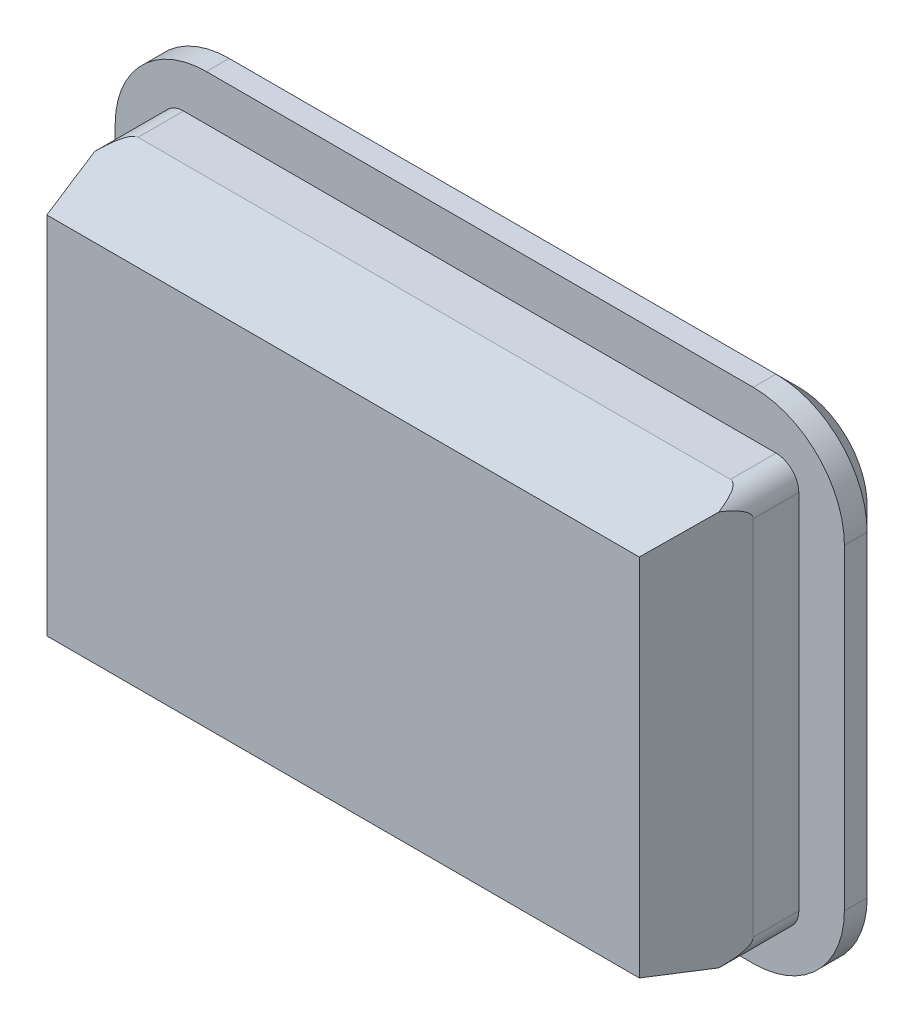
SolidWorks part; units mm, degrees
ref_plane "Front Plane" through (0, 0, 0) normal (0, 0, 1) x (1, 0, 0)
ref_plane "Top Plane" through (0, 0, 0) normal (0, 1, 0) x (1, 0, 0)
ref_plane "Right Plane" through (0, 0, 0) normal (1, 0, 0) x (0, 0, -1)
sketch "Sketch1" plane through (0, 0, 0) normal (0, 0, 1) x (1, 0, 0)
  line L1 (-7, -4.475) -> (7, -4.475)
  line L2 (-7, -4.475) -> (-7, 4.475)
  line L3 (-7, 4.475) -> (7, 4.475)
  line L4 (7, -4.475) -> (7, 4.475)
  line L5 (-7, -4.475) -> (7, 4.475) construction
  line L6 (-7, 4.475) -> (7, -4.475) construction
  point P0 (0, 0)
  dimension "D1" = 14
  dimension "D2" = 8.95
ref_plane "Plane1" through (0, 0, 2) normal (0, 0, 1) x (1, 0, 0)
sketch "Sketch2" plane through (0, 0, 2) normal (0, 0, 1) x (1, 0, 0)
  line L1 (-6.5, -4) -> (6.5, -4)
  line L2 (-6.5, -4) -> (-6.5, 4)
  line L3 (-6.5, 4) -> (6.5, 4)
  line L4 (6.5, -4) -> (6.5, 4)
  line L5 (-6.5, -4) -> (6.5, 4) construction
  line L6 (-6.5, 4) -> (6.5, -4) construction
  point P0 (0, 0)
  dimension "D1" = 13
  dimension "D2" = 8
loft "Loft1" add profiles "Sketch2", "Sketch1"
sketch "Sketch3" plane through (0, 0, 0) normal (0, 0, -1) x (-1, 0, 0)
  line L4 (-7, 4.475) -> (-7, -4.475)
  line L5 (-7, -4.475) -> (7, -4.475)
  line L6 (7, -4.475) -> (7, 4.475)
  line L7 (7, 4.475) -> (-7, 4.475)
  line L8 (-7, 4.475) -> (-7, -4.475)
  line L9 (-7, -4.475) -> (7, -4.475)
  line L10 (7, -4.475) -> (7, 4.475)
  line L11 (7, 4.475) -> (-7, 4.475)
  dimension "D1" = 0
extrude "Boss-Extrude1" add sketch "Sketch3" along normal blind 1
sketch "Sketch4" plane through (0, 0, -1) normal (0, 0, -1) x (-1, 0, 0)
  line L0 (7, 4.475) -> (-7, 4.475) construction
  line L1 (-8, -5.475) -> (8, -5.475)
  line L2 (-8, -5.475) -> (-8, 5.475)
  line L3 (-8, 5.475) -> (8, 5.475)
  line L4 (8, -5.475) -> (8, 5.475)
  line L5 (-8, -5.475) -> (8, 5.475) construction
  line L6 (-8, 5.475) -> (8, -5.475) construction
  line L7 (7, -4.475) -> (7, 4.475) construction
  point P0 (0, 0)
  dimension "D1" = 1
  dimension "D2" = 1
extrude "Boss-Extrude2" add sketch "Sketch4" along normal blind 1
fillet "Fillet1" radius 2 4 edges at (-8, -5.475, -1.5) (-8, 5.475, -1.5) (8, -5.475, -1.5) (8, 5.475, -1.5)
chamfer "Chamfer1" distance 0.5 angle 45 8 edges at (0, -5.475, -2) (-7.4142, -4.8892, -2) (7.4142, -4.8892, -2) (-8, 0, -2) (8, 0, -2) (-7.4142, 4.8892, -2) (7.4142, 4.8892, -2) (0, 5.475, -2)
fillet "Fillet2" radius 0.5 4 edges
